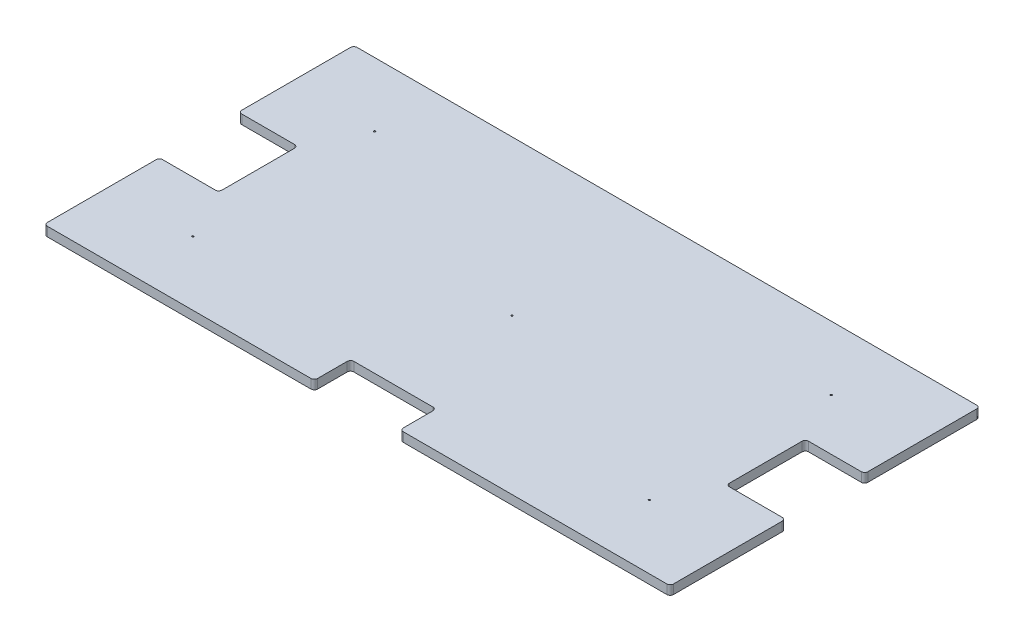
SolidWorks part; units mm, degrees
ref_plane "Front Plane" through (0, 0, 0) normal (0, 0, 1) x (1, 0, 0)
ref_plane "Top Plane" through (0, 0, 0) normal (0, 1, 0) x (1, 0, 0)
ref_plane "Right Plane" through (0, 0, 0) normal (1, 0, 0) x (0, 0, -1)
sketch "Sketch1" plane through (0, 0, 0) normal (0, 1, 0) x (1, 0, 0)
  line L1 (-603.25, -298.45) -> (603.25, -298.45)
  line L2 (-603.25, -298.45) -> (-603.25, 298.45)
  line L3 (-603.25, 298.45) -> (603.25, 298.45)
  line L4 (603.25, -298.45) -> (603.25, 298.45)
  line L5 (-603.25, -298.45) -> (603.25, 298.45) construction
  line L6 (-603.25, 298.45) -> (603.25, -298.45) construction
  point P0 (0, 0)
  dimension "D1" = 1206.5
  dimension "D2" = 596.9
extrude "Boss-Extrude1" add sketch "Sketch1" along normal blind 17.78
hole_wizard "1/8 (0.125) Diameter Hole1" positions "Sketch2" profile "Sketch3" hole size "1/8" standard "ANSI Inch"
sketch "Sketch2" plane through (0, 17.78, 0) normal (0, 1, 0) x (1, 0, 0)
  line L1 (-457.2, -152.4) -> (457.2, -152.4) construction
  line L2 (-457.2, -152.4) -> (-457.2, 152.4) construction
  line L3 (-457.2, 152.4) -> (457.2, 152.4) construction
  line L4 (457.2, -152.4) -> (457.2, 152.4) construction
  line L5 (-457.2, -152.4) -> (457.2, 152.4) construction
  line L6 (-457.2, 152.4) -> (457.2, -152.4) construction
  point P0 (0, 0)
  point P1 (457.2, 152.4)
  point P50 (-457.2, -152.4)
  point P51 (-457.2, 152.4)
  point P52 (457.2, -152.4)
  point P63 (0, 0)
  dimension "D1" = 914.4
  dimension "D2" = 304.8
sketch "Sketch3" plane through (0, 17.78, 0) normal (1, 0, 0) x (0, 0, 1)
  line L0 (0, 0) -> (0, 17.78)
  line L1 (0, 17.78) -> (1.5875, 17.78)
  line L2 (1.5875, 17.78) -> (1.5875, 0)
  line L5 (1.5875, 0) -> (0, 0)
  line L11 (0, -6.35) -> (0, 107.95) construction
  dimension "Thru Hole Dia." = 3.175
  dimension "Thru Hole Depth" = 17.78
fillet "Fillet1" radius 6.35 4 edges at (603.25, 8.89, -298.45) (603.25, 8.89, 298.45) (-603.25, 8.89, 298.45) (-603.25, 8.89, -298.45)
sketch "Sketch4" plane through (0, 17.78, 0) normal (0, 1, 0) x (1, 0, 0)
  line L0 (0, 298.45) -> (0, -298.45) construction
  line L1 (596.9, 298.45) -> (-596.9, 298.45) construction
  line L2 (-596.9, -298.45) -> (596.9, -298.45) construction
  line L3 (-603.25, 0) -> (603.25, 0) construction
  line L4 (-82.55, -228.6) -> (82.55, -228.6)
  line L5 (-82.55, -228.6) -> (-82.55, -298.45)
  line L6 (-82.55, -298.45) -> (82.55, -298.45)
  line L7 (82.55, -228.6) -> (82.55, -298.45)
  line L8 (-82.55, -228.6) -> (82.55, -298.45) construction
  line L9 (-82.55, -298.45) -> (82.55, -228.6) construction
  line L10 (-603.25, 292.1) -> (-603.25, -292.1) construction
  line L11 (603.25, -292.1) -> (603.25, 292.1) construction
  line L13 (-488.95, 76.2) -> (-603.25, 76.2)
  line L14 (-488.95, 76.2) -> (-488.95, -76.2)
  line L15 (-488.95, -76.2) -> (-603.25, -76.2)
  line L16 (-603.25, 76.2) -> (-603.25, -76.2)
  line L17 (-488.95, 76.2) -> (-603.25, -76.2) construction
  line L18 (-488.95, -76.2) -> (-603.25, 76.2) construction
  line L19 (488.95, 76.2) -> (603.25, 76.2)
  line L20 (488.95, 76.2) -> (488.95, -76.2)
  line L21 (488.95, -76.2) -> (603.25, -76.2)
  line L22 (603.25, 76.2) -> (603.25, -76.2)
  line L23 (488.95, 76.2) -> (603.25, -76.2) construction
  line L24 (488.95, -76.2) -> (603.25, 76.2) construction
  point P6 (0, -263.525)
  point P17 (-546.1, 0)
  point P22 (546.1, 0)
  dimension "D1" = 165.1
  dimension "D2" = 69.85
  dimension "D3" = 152.4
  dimension "D4" = 114.3
extrude "Cut-Extrude1" cut sketch "Sketch4" against normal through all
fillet "Fillet2" radius 6.35 12 edges at (82.55, 8.89, 298.45) (-82.55, 8.89, 298.45) (-82.55, 8.89, 228.6) (82.55, 8.89, 228.6) (-603.25, 8.89, 76.2) (-603.25, 8.89, -76.2) (-488.95, 8.89, 76.2) (-488.95, 8.89, -76.2) (603.25, 8.89, 76.2) (488.95, 8.89, 76.2) (488.95, 8.89, -76.2) (603.25, 8.89, -76.2)
hole_wizard "1/8 (0.125) Diameter Hole2" positions "Sketch5" profile "Sketch6" hole size "1/8" standard "ANSI Inch" end condition through all
sketch "Sketch5" plane through (0, 0, 0) normal (0, -1, 0) x (-1, 0, 0)
  point P0 (-439.8656, 175.259)
  point P3 (439.8656, 175.259)
  point P6 (439.8656, -175.259)
  point P9 (0, 0)
  point P12 (-439.8656, -175.259)
sketch "Sketch6" plane through (439.8656, 0, -175.259) normal (1, 0, 0) x (0, 0, -1)
  line L0 (0, 0) -> (0, 17.78)
  line L1 (0, 17.78) -> (1.5875, 17.78)
  line L2 (1.5875, 17.78) -> (1.5875, 0)
  line L5 (1.5875, 0) -> (0, 0)
  line L11 (0, -6.35) -> (0, 107.95) construction
  dimension "Thru Hole Dia." = 3.175
  dimension "Thru Hole Depth" = 17.78
